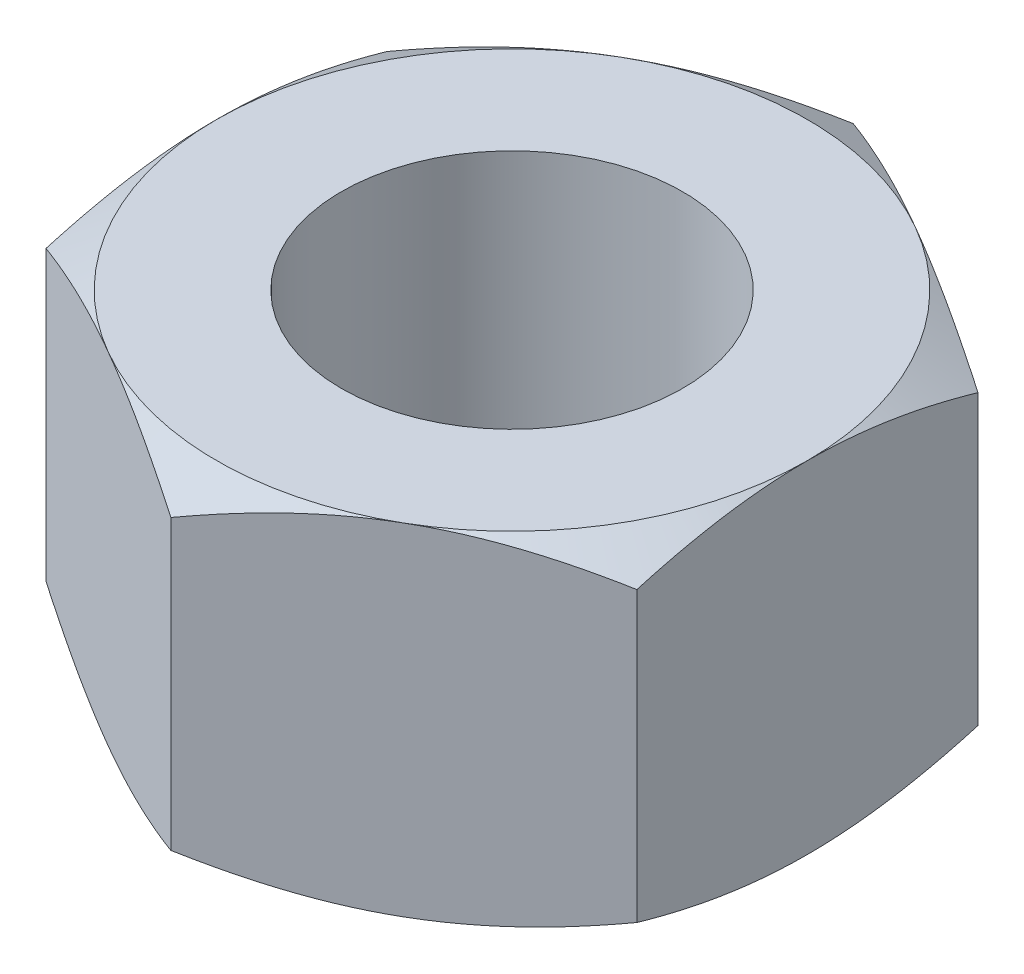
SolidWorks part; units mm, degrees
ref_plane "Front Plane" through (0, 0, 0) normal (0, 0, 1) x (1, 0, 0)
ref_plane "Top Plane" through (0, 0, 0) normal (0, 1, 0) x (1, 0, 0)
ref_plane "Right Plane" through (0, 0, 0) normal (1, 0, 0) x (0, 0, -1)
sketch "Sketch1" plane through (0, 0, 0) normal (0, 1, 0) x (1, 0, 0)
  line L1 (7.7942, 4.5) -> (0, 9)
  line L2 (0, 9) -> (-7.7942, 4.5)
  line L3 (-7.7942, 4.5) -> (-7.7942, -4.5)
  line L4 (-7.7942, -4.5) -> (0, -9)
  line L5 (0, -9) -> (7.7942, -4.5)
  line L6 (7.7942, -4.5) -> (7.7942, 4.5)
  circle A0 centre (0, 0) radius 7.7942 construction
  circle A1 centre (0, 0) radius 4.5
  dimension "D1" = 9
  dimension "D2" = 9
  dimension "D3" = 9
  dimension "D4" = 9
  dimension "D5" = 9
  dimension "D6" = 9
  dimension "D7" = 9
extrude "Boss-Extrude1" add sketch "Sketch1" along normal blind 9
sketch "Sketch2" plane through (0, 0, 0) normal (0, 1, 0) x (1, 0, 0)
  circle A0 centre (0, 0) radius 7.7942
  dimension "D1" = 15.5885
extrude "Cut-Extrude3" cut sketch "Sketch2" against normal mid plane 2 draft 60 flip side to cut contours A0
ref_plane "Plane1" through (0, 4.5, 0) normal (0, 1, 0) x (1, 0, 0)
mirror "Mirror2" about plane through (0, 4.5, 0) normal (0, 1, 0) of "Cut-Extrude3"
